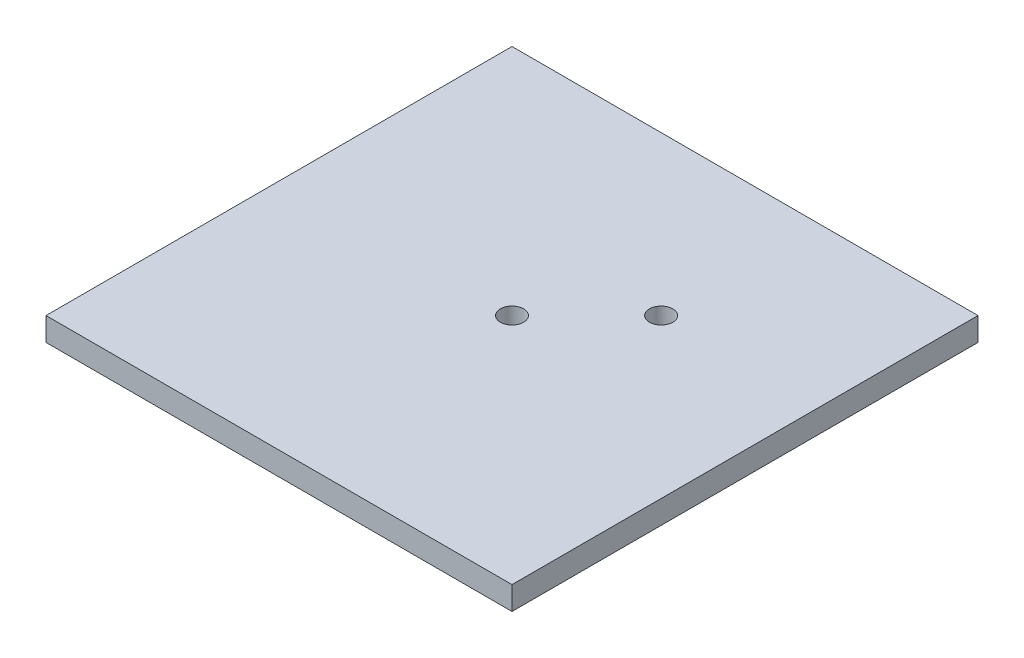
SolidWorks part; units mm, degrees
ref_plane "前视基准面" through (0, 0, 0) normal (0, 0, 1) x (1, 0, 0)
ref_plane "上视基准面" through (0, 0, 0) normal (0, 1, 0) x (1, 0, 0)
ref_plane "右视基准面" through (0, 0, 0) normal (1, 0, 0) x (0, 0, -1)
sketch "草图1" plane through (0, 0, 0) normal (0, 1, 0) x (1, 0, 0)
  line L0 (-28.1898, 0) -> (29.8139, 0) construction
  line L1 (0, 21.2293) -> (0, -20.3676) construction
  line L3 (50, -50) -> (-50, -50)
  line L4 (50, -50) -> (50, 50)
  line L5 (50, 50) -> (-50, 50)
  line L6 (-50, -50) -> (-50, 50)
  line L7 (50, -50) -> (-50, 50) construction
  line L8 (50, 50) -> (-50, -50) construction
  circle A0 centre (0, 0) radius 2.5
  circle A1 centre (16, 16) radius 2.5
  point P5 (0, 0)
  point P14 (0, 0)
  point P15 (12.8768, 9.3966)
  point P16 (0, 0)
  point P17 (0, 0)
  dimension "D1" = 5
  dimension "D2" = 5
  dimension "D3" = 16
  dimension "D4" = 16
  dimension "D5" = 100
  dimension "D6" = 100
extrude "凸台-拉伸1" add sketch "草图1" along normal blind 5
